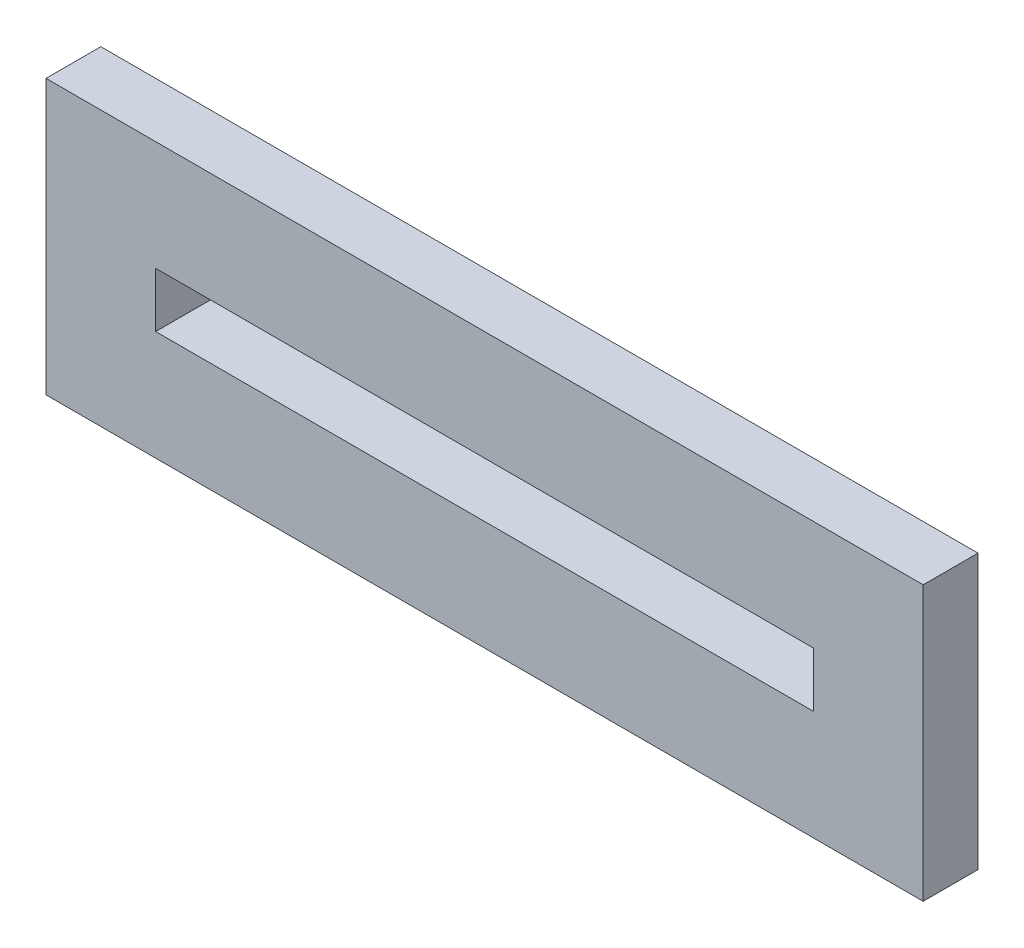
SolidWorks part; units mm, degrees
ref_plane "Front" through (0, 0, 0) normal (0, 0, 1) x (1, 0, 0)
ref_plane "Top" through (0, 0, 0) normal (0, 1, 0) x (1, 0, 0)
ref_plane "Right" through (0, 0, 0) normal (1, 0, 0) x (0, 0, -1)
sketch "Sketch1" plane through (0, 0, 0) normal (0, 0, 1) x (1, 0, 0)
  line L1 (0, 0) -> (38.1, 0)
  line L2 (0, 0) -> (0, -3.175)
  line L3 (0, -3.175) -> (38.1, -3.175)
  line L4 (38.1, 0) -> (38.1, -3.175)
  line L5 (-6.35, 6.35) -> (44.45, 6.35)
  line L6 (-6.35, 6.35) -> (-6.35, -9.525)
  line L7 (-6.35, -9.525) -> (44.45, -9.525)
  line L8 (44.45, 6.35) -> (44.45, -9.525)
  point P9 (19.05, 0)
  point P10 (19.05, 6.35)
  point P11 (38.1, -1.5875)
  point P12 (44.45, -1.5875)
  dimension "D1" = 38.1
  dimension "D2" = 3.175
  dimension "D3" = 6.35
  dimension "D4" = 6.35
extrude "Boss-Extrude1" add sketch "Sketch1" along normal blind 3.175
